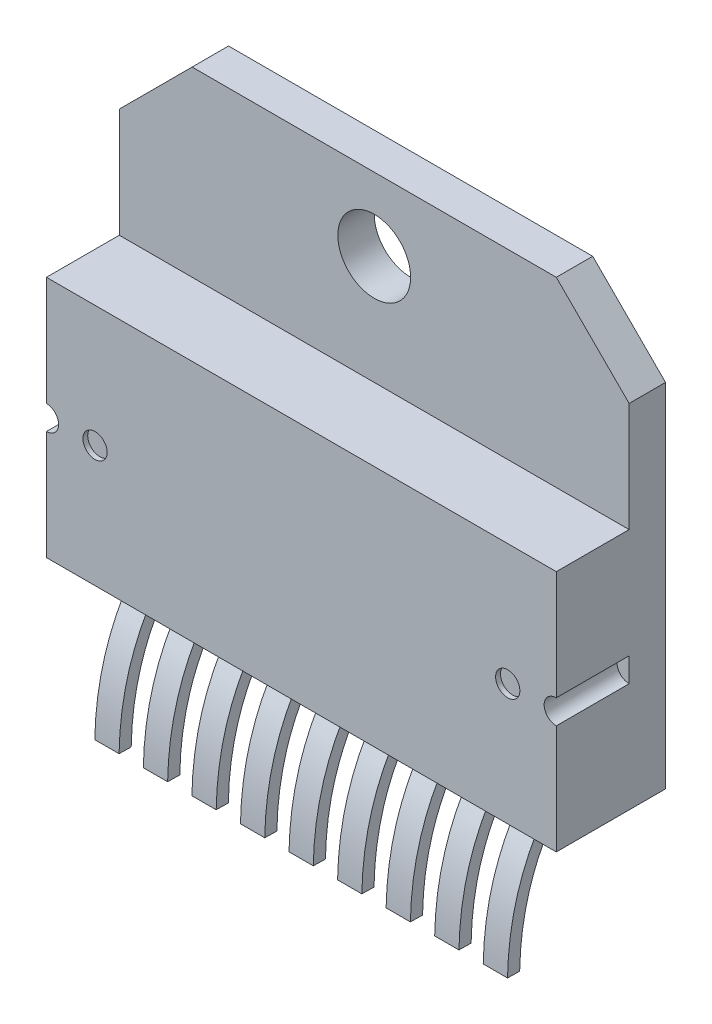
SolidWorks part; units mm, degrees
ref_plane "Ön Düzlem" through (0, 0, 0) normal (0, 0, 1) x (1, 0, 0)
ref_plane "Üst Düzlem" through (0, 0, 0) normal (0, 1, 0) x (1, 0, 0)
ref_plane "Sağ Düzlem" through (0, 0, 0) normal (1, 0, 0) x (0, 0, -1)
sketch "Çizim1" plane through (0, 0, 0) normal (0, 0, 1) x (1, 0, 0)
  line L0 (-10.5, 5.75) -> (-7.5, 8.75)
  line L1 (-7.5, 8.75) -> (7.5, 8.75)
  line L2 (-10.5, 5.75) -> (-10.5, -8.75)
  line L3 (-10.5, -8.75) -> (10.5, -8.75)
  line L4 (10.5, 5.75) -> (10.5, -8.75)
  line L5 (-10.5, 8.75) -> (10.5, -8.75) construction
  line L6 (-10.5, -8.75) -> (10.5, 8.75) construction
  line L7 (7.5, 8.75) -> (10.5, 5.75)
  point P0 (0, 0)
  dimension "D1" = 21
  dimension "D2" = 17.5
extrude "Yükseklik-Ekstrüzyon1" add sketch "Çizim1" along normal blind 1.5
sketch "Çizim2" plane through (0, 0, 1.5) normal (0, 0, 1) x (1, 0, 0)
  line L0 (10.5, -8.75) -> (10.5, 5.75) construction
  line L1 (-10.5, -8.75) -> (10.5, -8.75)
  line L2 (-10.5, -8.75) -> (-10.5, 1.25)
  line L3 (-10.5, 1.25) -> (10.5, 1.25)
  line L4 (10.5, -8.75) -> (10.5, 1.25)
  dimension "D1" = 10
extrude "Yükseklik-Ekstrüzyon2" add sketch "Çizim2" along normal blind 3
sketch "Çizim3" plane through (0, 0, 4.5) normal (0, 0, 1) x (1, 0, 0)
  line L0 (-10.5, -3.75) -> (10.5, -3.75) construction
  line L1 (-10.5, 1.25) -> (-10.5, -8.75) construction
  line L2 (10.5, -8.75) -> (10.5, 1.25) construction
  line L3 (-10.5, -3.25) -> (-10.5, -4.25)
  line L4 (0, -3.75) -> (0, -2.0756) construction
  line L5 (10.5, -3.25) -> (10.5, -4.25)
  arc A0 (-10.5, -4.25) -> (-10.5, -3.25) centre (-10.5, -3.75) ccw
  arc A1 (10.5, -4.25) -> (10.5, -3.25) centre (10.5, -3.75) cw
  dimension "D1" = 1
extrude "Kes-Ekstrüzyon1" cut sketch "Çizim3" against normal blind 3
sketch "Çizim4" plane through (0, 0, 4.5) normal (0, 0, 1) x (1, 0, 0)
  line L0 (-10, -3.75) -> (10, -3.75) construction
  line L1 (-10.5, 1.25) -> (-10.5, -3.25) construction
  line L2 (0, -3.75) -> (0, -1.8739) construction
  arc A0 (-10.5, -4.25) -> (-10.5, -3.25) centre (-10.5, -3.75) ccw construction
  arc A1 (10.5, -3.25) -> (10.5, -4.25) centre (10.5, -3.75) ccw construction
  circle A2 centre (-8.5, -3.75) radius 0.5
  circle A3 centre (8.5, -3.75) radius 0.5
  dimension "D1" = 1
  dimension "D2" = 2
extrude "Kes-Ekstrüzyon2" cut sketch "Çizim4" against normal blind 0.2
sketch "Çizim5" plane through (0, 0, 0) normal (1, 0, 0) x (0, 0, -1)
  line L0 (-2.25, -14.25) -> (-2.25, -8.25) construction
  line L3 (-2.25, -14.25) -> (-4.5, -14.25) construction
  line L4 (-2.1211, -8.115) -> (-1.7633, -8.4642)
  line L5 (-4.5, -14.25) -> (-4.0001, -14.2593)
  spline S0 degree 2 poles (-4.5, -14.25) (-4.4299, -10.4799) (-2.1211, -8.115) knots 0 0 0 1 1 1
  spline S1 degree 1 poles (-4.0001, -14.2593) (-1.7633, -8.4642) knots 0 0 1 1 construction
  spline S2 degree 3 poles (-4.0001, -14.2593) (-3.9946, -13.9651) (-3.9608, -13.3667) (-3.8055, -12.2595) (-3.4462, -10.9811) (-2.762, -9.6322) (-2.1184, -8.828) (-1.7633, -8.4642) knots 0 0 0 0 0.125 0.25 0.5 0.75 1 1 1 1
  dimension "D1" = 6
  dimension "D2" = 0.5
extrude "Yükseklik-Ekstrüzyon3" add sketch "Çizim5" along normal blind 10 and the other way blind 10
ref_plane "Düzlem1" through (0, 0, 7) normal (0, 0, 1) x (1, 0, 0)
sketch "Çizim8" plane through (0, 0, 7) normal (0, 0, 1) x (1, 0, 0)
  line L0 (0, -8.75) -> (0, -14.25) construction
  line L1 (-10.5, -8.75) -> (10.5, -8.75) construction
  line L2 (-10, -14.25) -> (10, -14.25) construction
  line L3 (0.9904, -8.75) -> (0.9904, -14.25) construction
  line L4 (2.4904, -8.75) -> (2.4904, -14.25)
  line L5 (0.4904, -8.75) -> (1.4904, -8.75)
  line L6 (0.4904, -8.75) -> (0.4904, -14.25)
  line L8 (1.4904, -8.75) -> (1.4904, -14.25)
  line L9 (0.4904, -8.75) -> (1.4904, -14.25) construction
  line L10 (0.4904, -14.25) -> (1.4904, -8.75) construction
  line L11 (2.4904, -8.75) -> (3.4904, -8.75)
  line L12 (3.4904, -8.75) -> (3.4904, -14.25)
  line L14 (4.4904, -8.75) -> (4.4904, -14.25)
  line L15 (4.4904, -8.75) -> (5.4904, -8.75)
  line L16 (5.4904, -8.75) -> (5.4904, -14.25)
  line L18 (6.4904, -8.75) -> (6.4904, -14.25)
  line L19 (6.4904, -8.75) -> (7.4904, -8.75)
  line L20 (7.4904, -8.75) -> (7.4904, -14.25)
  line L22 (8.4904, -8.75) -> (8.4904, -14.25)
  line L26 (8.4904, -8.75) -> (9.4904, -8.75) [skipped]
  line L28 (9.4904, -8.75) -> (9.4904, -14.25) [skipped]
  line L29 (8.4904, -8.75) -> (10, -8.75)
  line L30 (10, -8.75) -> (10, -14.25)
  line L32 (-1.5096, -8.75) -> (-1.5096, -14.25)
  line L33 (-1.5096, -8.75) -> (-0.5096, -8.75)
  line L34 (-0.5096, -8.75) -> (-0.5096, -14.25)
  line L36 (0.4904, -8.75) -> (0.4904, -14.25)
  line L38 (1.4904, -8.75) -> (1.4904, -14.25)
  line L39 (0.4904, -8.75) -> (1.4904, -8.75)
  line L40 (2.4904, -8.75) -> (2.4904, -14.25)
  line L42 (3.4904, -8.75) -> (3.4904, -14.25)
  line L43 (2.4904, -8.75) -> (3.4904, -8.75)
  line L44 (4.4904, -8.75) -> (4.4904, -14.25)
  line L46 (5.4904, -8.75) -> (5.4904, -14.25)
  line L47 (4.4904, -8.75) -> (5.4904, -8.75)
  line L48 (-3.5096, -8.75) -> (-3.5096, -14.25)
  line L49 (-3.5096, -8.75) -> (-2.5096, -8.75)
  line L50 (-2.5096, -8.75) -> (-2.5096, -14.25)
  line L52 (-1.5096, -8.75) -> (-1.5096, -14.25)
  line L54 (-0.5096, -8.75) -> (-0.5096, -14.25)
  line L55 (-1.5096, -8.75) -> (-0.5096, -8.75)
  line L56 (0.4904, -8.75) -> (0.4904, -14.25)
  line L58 (1.4904, -8.75) -> (1.4904, -14.25)
  line L59 (0.4904, -8.75) -> (1.4904, -8.75)
  line L60 (2.4904, -8.75) -> (2.4904, -14.25)
  line L62 (3.4904, -8.75) -> (3.4904, -14.25)
  line L63 (2.4904, -8.75) -> (3.4904, -8.75)
  line L64 (-5.5096, -8.75) -> (-5.5096, -14.25)
  line L65 (-5.5096, -8.75) -> (-4.5096, -8.75)
  line L66 (-4.5096, -8.75) -> (-4.5096, -14.25)
  line L68 (-3.5096, -8.75) -> (-3.5096, -14.25)
  line L70 (-2.5096, -8.75) -> (-2.5096, -14.25)
  line L71 (-3.5096, -8.75) -> (-2.5096, -8.75)
  line L72 (-1.5096, -8.75) -> (-1.5096, -14.25)
  line L74 (-0.5096, -8.75) -> (-0.5096, -14.25)
  line L75 (-1.5096, -8.75) -> (-0.5096, -8.75)
  line L76 (0.4904, -8.75) -> (0.4904, -14.25)
  line L78 (1.4904, -8.75) -> (1.4904, -14.25)
  line L79 (0.4904, -8.75) -> (1.4904, -8.75)
  line L80 (-7.5096, -8.75) -> (-7.5096, -14.25)
  line L81 (-7.5096, -8.75) -> (-6.5096, -8.75)
  line L82 (-6.5096, -8.75) -> (-6.5096, -14.25)
  line L84 (-5.5096, -8.75) -> (-5.5096, -14.25)
  line L86 (-4.5096, -8.75) -> (-4.5096, -14.25)
  line L87 (-5.5096, -8.75) -> (-4.5096, -8.75)
  line L88 (-3.5096, -8.75) -> (-3.5096, -14.25)
  line L90 (-2.5096, -8.75) -> (-2.5096, -14.25)
  line L91 (-3.5096, -8.75) -> (-2.5096, -8.75)
  line L92 (-1.5096, -8.75) -> (-1.5096, -14.25)
  line L94 (-0.5096, -8.75) -> (-0.5096, -14.25)
  line L95 (-1.5096, -8.75) -> (-0.5096, -8.75)
  line L98 (-8.5096, -8.75) -> (-8.5096, -14.25)
  line L100 (-7.5096, -8.75) -> (-7.5096, -14.25)
  line L102 (-6.5096, -8.75) -> (-6.5096, -14.25)
  line L103 (-7.5096, -8.75) -> (-6.5096, -8.75)
  line L104 (-5.5096, -8.75) -> (-5.5096, -14.25)
  line L106 (-4.5096, -8.75) -> (-4.5096, -14.25)
  line L107 (-5.5096, -8.75) -> (-4.5096, -8.75)
  line L108 (-3.5096, -8.75) -> (-3.5096, -14.25)
  line L110 (-2.5096, -8.75) -> (-2.5096, -14.25)
  line L111 (-3.5096, -8.75) -> (-2.5096, -8.75)
  line L112 (-9.5096, -8.75) -> (-8.5096, -8.75) [skipped]
  line L114 (-9.5096, -8.75) -> (-9.5096, -14.25) [skipped]
  line L115 (-8.5096, -8.75) -> (-10, -8.75)
  line L116 (-10, -8.75) -> (-10, -14.25)
  line L118 (-8.5096, -14.25) -> (-8.5096, -14.9397)
  line L120 (-10, -14.25) -> (-10, -14.9397)
  line L121 (-10, -14.9397) -> (-8.5096, -14.9397)
  line L122 (10, -14.25) -> (10, -14.9397)
  line L123 (-1.5096, -14.25) -> (-1.5096, -14.9397)
  line L133 (-1.5096, -14.9397) -> (-0.5096, -14.9397)
  line L138 (-0.5096, -14.9397) -> (-0.5096, -14.25)
  line L144 (0.4904, -14.25) -> (0.4904, -14.9397)
  line L145 (1.4904, -14.25) -> (1.4904, -14.9397)
  line L148 (-7.5096, -14.25) -> (-7.5096, -14.9397)
  line L149 (-7.5096, -14.9397) -> (-6.5096, -14.9397)
  line L150 (-6.5096, -14.9397) -> (-6.5096, -14.25)
  line L151 (-5.5096, -14.25) -> (-5.5096, -14.9397)
  line L152 (-5.5096, -14.9397) -> (-4.5096, -14.9397)
  line L153 (-4.5096, -14.9397) -> (-4.5096, -14.25)
  line L154 (-3.5096, -14.25) -> (-3.5096, -14.9397)
  line L155 (-3.5096, -14.9397) -> (-2.5096, -14.9397)
  line L156 (-2.5096, -14.9397) -> (-2.5096, -14.25)
  line L157 (2.4904, -14.9397) -> (2.4904, -14.25)
  line L158 (2.4904, -14.9397) -> (3.4904, -14.9397)
  line L159 (3.4904, -14.9397) -> (3.4904, -14.25)
  line L160 (4.4904, -14.25) -> (4.4904, -14.9397)
  line L161 (4.4904, -14.9397) -> (5.4904, -14.9397)
  line L162 (5.4904, -14.9397) -> (5.4904, -14.25)
  line L164 (6.4904, -14.9397) -> (6.4904, -14.25)
  line L165 (6.4904, -14.9397) -> (7.4904, -14.9397)
  line L166 (7.4904, -14.9397) -> (7.4904, -14.25)
  line L168 (8.4904, -14.9397) -> (8.4904, -14.25)
  line L169 (-7.5096, -14.9397) -> (-6.5096, -14.9397)
  line L170 (-5.5096, -14.9397) -> (-4.5096, -14.9397)
  line L171 (-3.5096, -14.9397) -> (-2.5096, -14.9397)
  line L172 (-1.5096, -14.9397) -> (3.4904, -14.9397)
  line L173 (4.4904, -14.9397) -> (5.4904, -14.9397)
  line L174 (6.4904, -14.9397) -> (7.4904, -14.9397)
  line L175 (8.4904, -14.9397) -> (10, -14.9397)
  point P7 (0.9904, -11.5)
  dimension "D2" = 1
  dimension "D1" = 2
  dimension "D3" = 5
  dimension "D4" = 6
extrude "Kes-Ekstrüzyon3" cut sketch "Çizim8" against normal blind 10
sketch "Çizim9" plane through (0, 0, 1.5) normal (0, 0, 1) x (1, 0, 0)
  line L0 (-10.5, 5.75) -> (10.5, 5.75) construction
  line L1 (-10.5, 5.75) -> (-10.5, 1.25) construction
  line L2 (10.5, 1.25) -> (10.5, 5.75) construction
  line L3 (7.5, 8.75) -> (-7.5, 8.75) construction
  circle A0 centre (0, 5.75) radius 1.5
  dimension "D2" = 3
  dimension "D1" = 3
extrude "Kes-Ekstrüzyon4" cut sketch "Çizim9" against normal blind 10
